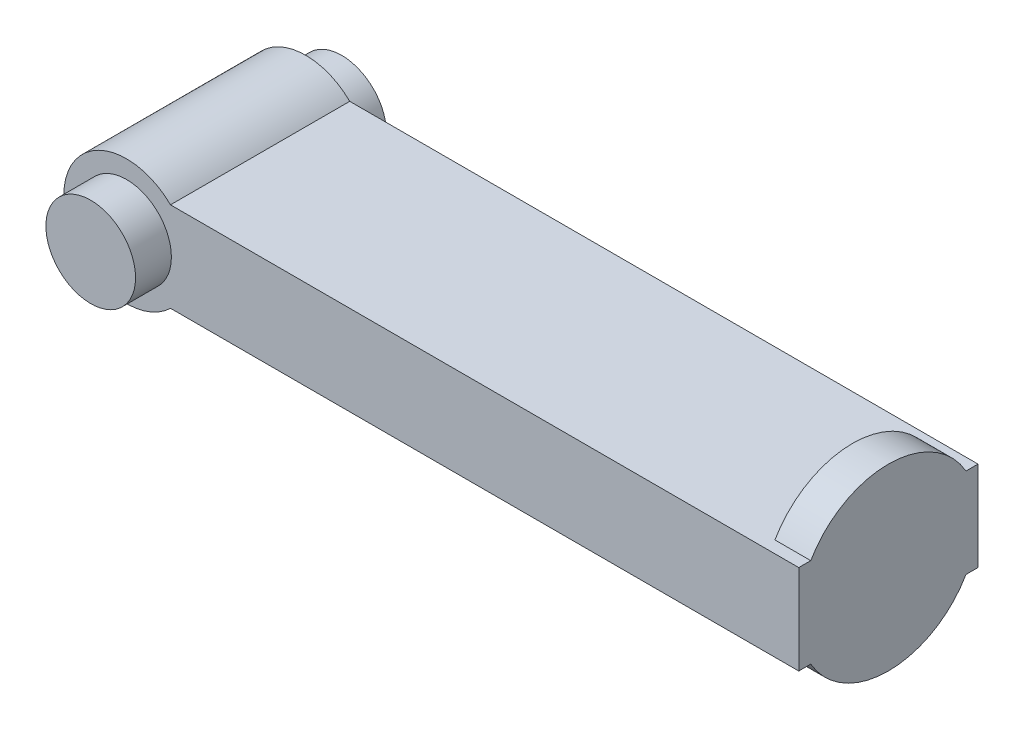
SolidWorks part; units mm, degrees
ref_plane "Front Plane" through (0, 0, 0) normal (0, 0, 1) x (1, 0, 0)
ref_plane "Top Plane" through (0, 0, 0) normal (0, 1, 0) x (1, 0, 0)
ref_plane "Right Plane" through (0, 0, 0) normal (1, 0, 0) x (0, 0, -1)
sketch "Sketch1" plane through (0, 0, 0) normal (0, 0, 1) x (1, 0, 0)
  line L1 (24.4949, 25) -> (375, 25)
  line L3 (24.4949, -25) -> (375, -25)
  line L4 (375, 25) -> (375, -25)
  arc A0 (24.4949, 25) -> (24.4949, -25) centre (0, 0) ccw
  point P8 (0, 0)
  point P9 (0, 0)
  point P10 (15.2886, -31.4843)
  dimension "D1" = 70
  dimension "D3" = 375
  dimension "D4" = 50
  dimension "D5" = 25
extrude "Boss-Extrude1" add sketch "Sketch1" along normal blind 100
sketch "Sketch2" plane through (375, 0, 0) normal (1, 0, 0) x (0, 0, -1)
  line L0 (-100, 25) -> (0, 25) construction
  circle A0 centre (-50, 0) radius 50
  point P4 (-50, 25)
  dimension "D1" = 100
extrude "Boss-Extrude2" add sketch "Sketch2" against normal blind 20
sketch "Sketch3" plane through (0, 0, 100) normal (0, 0, 1) x (1, 0, 0)
  circle A0 centre (0, 0) radius 25
  dimension "D1" = 50
extrude "Boss-Extrude3" add sketch "Sketch3" along normal blind 20 and the other way blind 120
